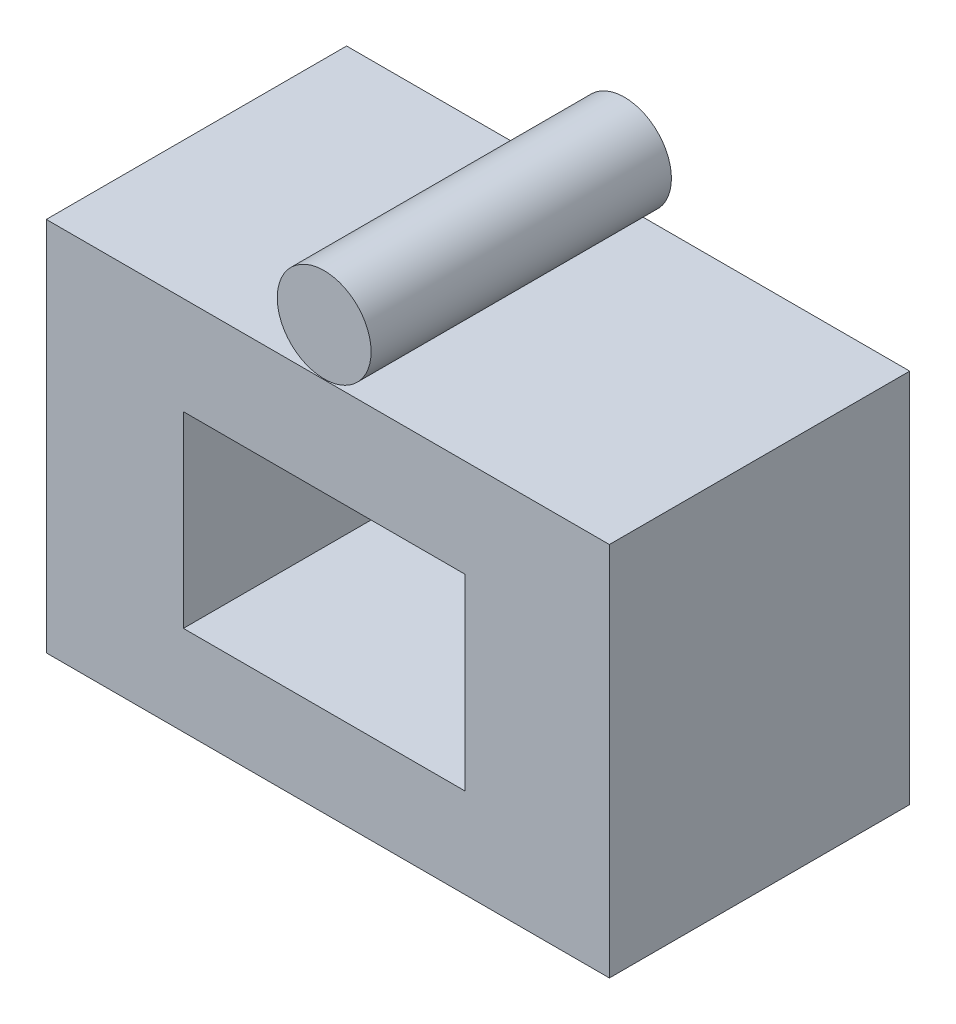
SolidWorks part; units mm, degrees
ref_plane "Plan de face" through (0, 0, 0) normal (0, 0, 1) x (1, 0, 0)
ref_plane "Plan de dessus" through (0, 0, 0) normal (0, 1, 0) x (1, 0, 0)
ref_plane "Plan de droite" through (0, 0, 0) normal (1, 0, 0) x (0, 0, -1)
sketch "Esquisse1" plane through (0, 0, 0) normal (0, 0, 1) x (1, 0, 0)
  line L1 (-62.3913, 40.9783) -> (87.6087, 40.9783)
  line L2 (-62.3913, 40.9783) -> (-62.3913, -59.0217)
  line L3 (-62.3913, -59.0217) -> (87.6087, -59.0217)
  line L4 (87.6087, 40.9783) -> (87.6087, -59.0217)
  line L5 (-25.8696, 14.8913) -> (49.1304, 14.8913)
  line L6 (-25.8696, 14.8913) -> (-25.8696, -35.1087)
  line L7 (-25.8696, -35.1087) -> (49.1304, -35.1087)
  line L8 (49.1304, 14.8913) -> (49.1304, -35.1087)
  dimension "D1" = 100
  dimension "D2" = 150
  dimension "D3" = 75
  dimension "D4" = 50
extrude "Boss.-Extru.1" add sketch "Esquisse1" along normal blind 80
sketch "Esquisse3" plane through (0, 0, 80) normal (0, 0, 1) x (1, 0, 0)
  line L0 (11.6304, 69.383) -> (11.6304, -64.4815) construction
  line L1 (-18.4699, 40.9783) -> (107.3012, 40.9783) construction
  line L2 (87.6087, 40.9783) -> (-62.3913, 40.9783) construction
  circle A0 centre (11.6304, 53.6818) radius 12.5
  dimension "D1" = 25
  dimension "D2" = 37.5
extrude "Boss.-Extru.2" add sketch "Esquisse3" against normal blind 80
sketch "Esquisse5" plane through (0, 0, 80) normal (0, 0, 1) x (1, 0, 0)
  line L0 (11.6304, 69.2211) -> (11.6304, -68.852) construction
  circle A0 centre (11.6304, 53.6818) radius 12.5 construction
  point P5 (11.6304, 66.1818)
